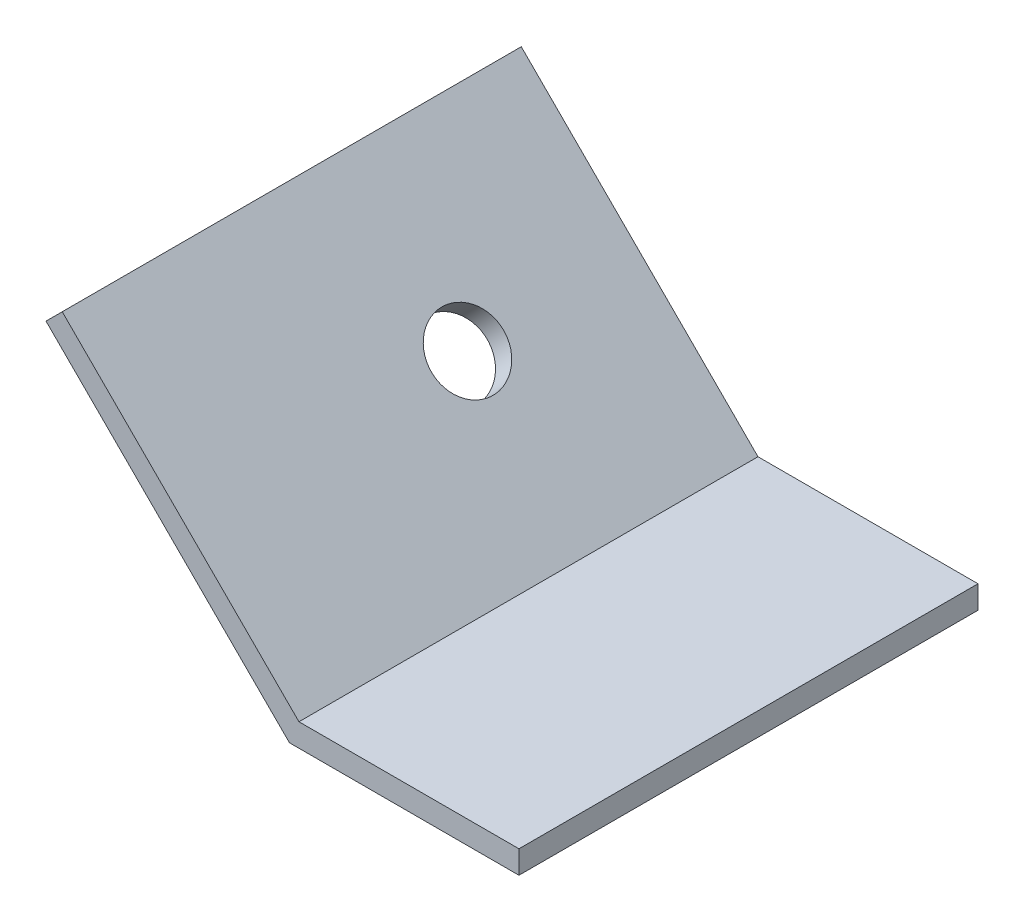
SolidWorks part; units mm, degrees
material "6061 Alloy"
ref_plane "Front Plane" through (0, 0, 0) normal (0, 0, 1) x (1, 0, 0)
ref_plane "Top Plane" through (0, 0, 0) normal (0, 1, 0) x (1, 0, 0)
ref_plane "Right Plane" through (0, 0, 0) normal (1, 0, 0) x (0, 0, -1)
sketch "Sketch1" plane through (0, 0, 0) normal (0, 0, 1) x (1, 0, 0)
  line L0 (-26.9408, 26.9408) -> (0, 0)
  line L1 (0, 0) -> (25.4, 0)
  dimension "D1" = 135
  dimension "D2" = 25.4
  dimension "D3" = 38.1
extrude "base" add sketch "Sketch1" along normal blind 50.8 thin thin type one direction reverse wall 2.54
sketch "Sketch2" plane through (1.7961, 1.7961, 0) normal (0.7071, 0.7071, 0) x (0, 0, -1)
  line L4 (0, 1.0521) -> (0, 38.1)
  line L5 (0, 38.1) -> (-50.8, 38.1)
  line L6 (-50.8, 38.1) -> (-50.8, 1.0521)
  line L7 (-50.8, 1.0521) -> (0, 1.0521)
  line L8 (0, 1.0521) -> (0, 38.1)
  line L9 (0, 38.1) -> (-50.8, 38.1)
  line L10 (-50.8, 38.1) -> (-50.8, 1.0521)
  line L11 (-50.8, 1.0521) -> (0, 1.0521)
  circle A0 centre (-19.05, 19.5761) radius 4
  point P4 (-25.4, 38.1)
  point P7 (-50.8, 19.5761)
  dimension "D1" = 8
  dimension "D3" = 19.05
  dimension "D2" = 0
extrude "axle hole" cut sketch "Sketch2" against normal up to next contours A0
